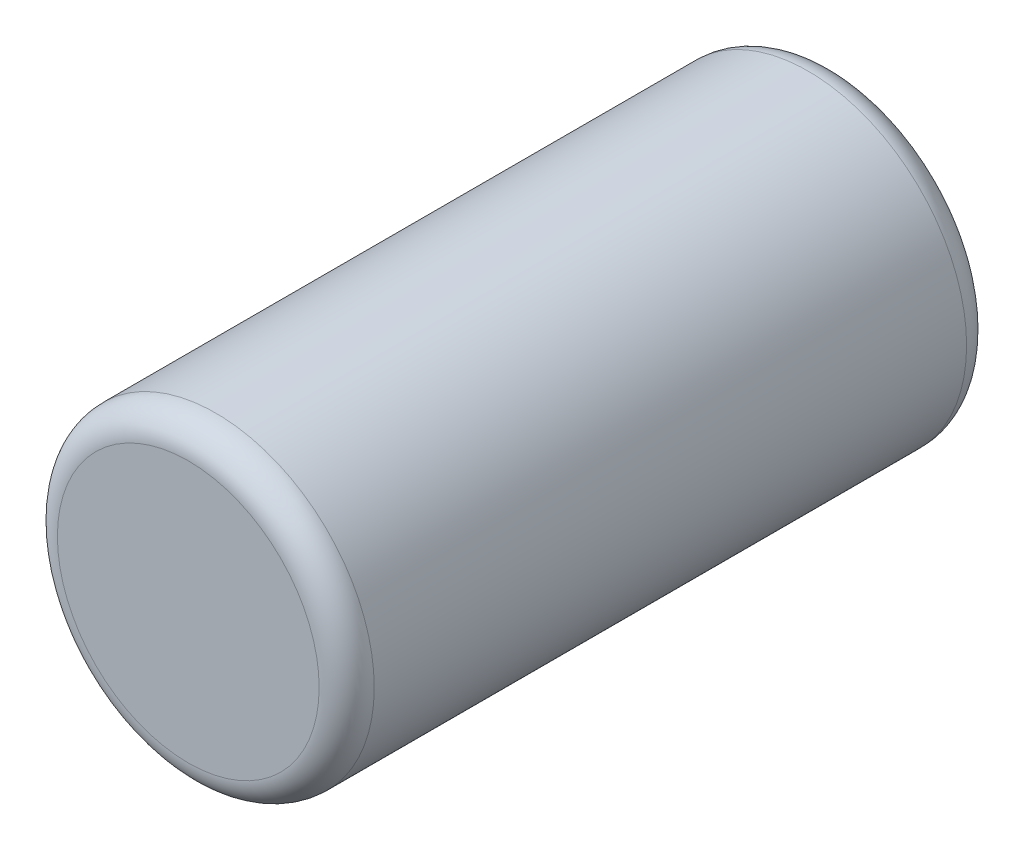
SolidWorks part; units mm, degrees
material "XC38"
ref_plane "Face" through (0, 0, 0) normal (0, 0, 1) x (1, 0, 0)
ref_plane "Dessus" through (0, 0, 0) normal (0, 1, 0) x (1, 0, 0)
ref_plane "Droite" through (0, 0, 0) normal (1, 0, 0) x (0, 0, -1)
sketch "Esquisse1" plane through (0, 0, 0) normal (0, 0, 1) x (1, 0, 0)
  circle A0 centre (0, 0) radius 5.75
  dimension "D1" = 11.5
extrude "Boss.-Extru.1" add sketch "Esquisse1" along normal mid plane 23.5
fillet "Congé1" radius 1 2 edges at (5.75, 0, -11.75) (5.75, 0, 11.75)
